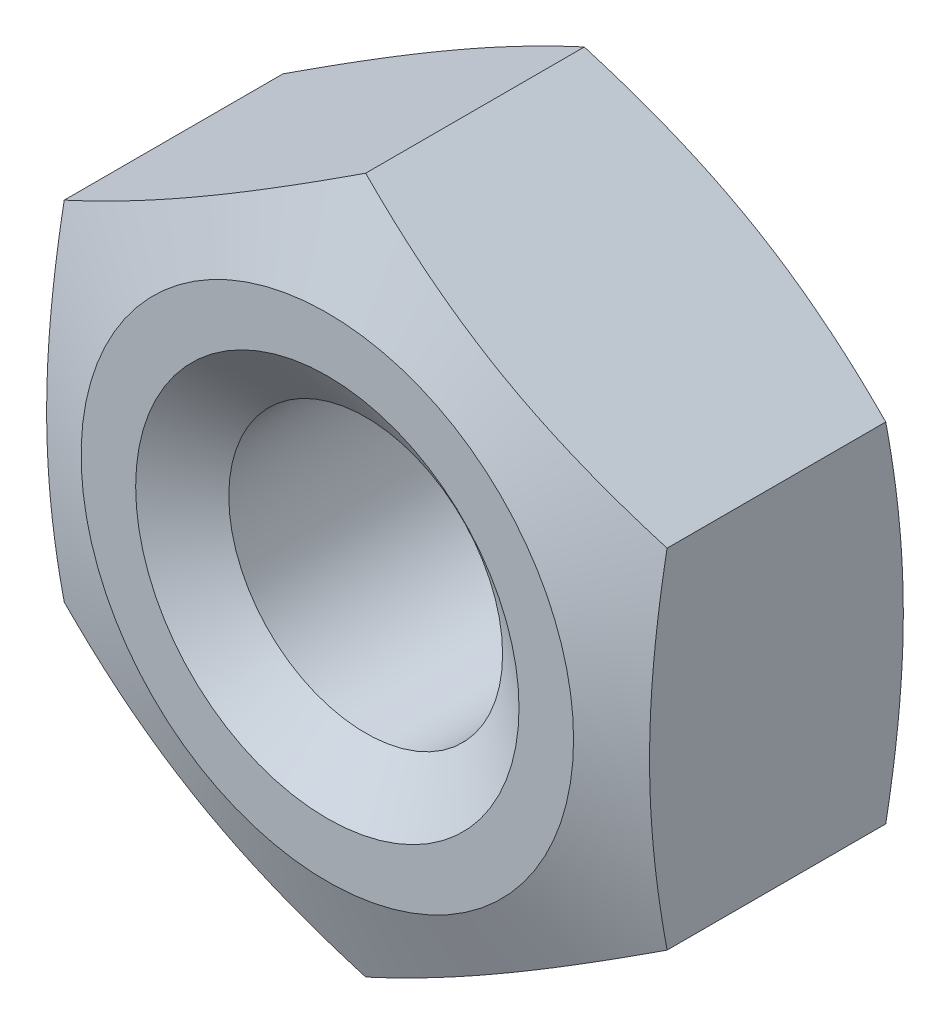
SolidWorks part; units mm, degrees
extrude "BaseNut" add sketch "BaseNutSke" against normal blind 8.5598
sketch "BaseNutSke" plane through (0, 0, 0) normal (0, 0, 1) x (1, 0, 0)
  line L0 (8.7376, 5.0447) -> (-8.7376, -5.0447) construction
  line L1 (-8.7376, 5.0447) -> (8.7376, -5.0447) construction
  line L2 (8.7376, -5.0447) -> (8.6272, -4.9539) construction
  line L3 (0, 10.0893) -> (0, -10.0893) construction
  line L6 (8.7376, 5.0447) -> (8.7376, -5.0447)
  line L7 (-8.7376, 5.0447) -> (-8.7376, -5.0447)
  line L8 (8.7376, 5.0447) -> (0, 10.0893)
  line L9 (0, 10.0893) -> (-8.7376, 5.0447)
  line L10 (-8.7376, -5.0447) -> (0, -10.0893)
  line L11 (0, -10.0893) -> (8.7376, -5.0447)
  circle A0 centre (0, 0) radius 3.9688
  dimension "D4" = 8.7376
  dimension "Tap_drill" = 7.9375
  dimension "D1" = 120
  dimension "D2" = 8.7376
  dimension "D3" = 8.7376
pattern_linear "ThdSchPat" [suppressed]
revolve "ThreadSchematic" [suppressed] cut sketch "ThdSchSke" angle 360 about L6
sketch "ThdSchSke" plane through (0, 0, 0) normal (0, 1, 0) x (1, 0, 0)
  line L0 (-5.5562, 0.0254) -> (-3.9688, 1.137)
  line L1 (-3.9688, 1.137) -> (-1.9844, 1.137)
  line L2 (-1.9844, 1.137) -> (-1.9844, -1.0862)
  line L3 (-1.9844, -1.0862) -> (-3.9688, -1.0862)
  line L4 (-3.9688, -1.0862) -> (-5.5562, 0.0254)
  line L5 (-3.175, 1.5875) -> (3.175, 1.5875) construction
  line L6 (0, 1.5875) -> (0, -2.9874) construction
  line L7 (0, 7.4228) -> (0, 1.1116) construction
  dimension "SideAngle" = 55
  dimension "Thread_major" = 11.1125
  dimension "Advance" = 1.5875
  dimension "D1" = 0.0254
ref_plane "Plane1" through (0, 0, 0) normal (0, 0, 1) x (1, 0, 0)
ref_plane "Plane2" through (0, 0, 0) normal (0, 1, 0) x (1, 0, 0)
ref_plane "Plane3" through (0, 0, 0) normal (1, 0, 0) x (0, 0, -1)
sketch "Sketch4" plane through (0, 0, 0) normal (1, 0, 0) x (0, 0, -1)
  line L0 (8.5598, 8.7376) -> (8.1534, 8.7376)
  line L1 (8.5598, 8.7376) -> (8.5598, 22.7893)
  line L2 (8.1534, 22.7893) -> (8.5598, 22.7893)
  line L3 (8.1534, 22.7893) -> (8.1534, 8.7376)
  line L4 (0, 0) -> (34.925, 0) construction
  line L6 (8.5598, 5.0447) -> (8.5598, 10.0893) construction
  line L7 (0, 8.7376) -> (-12.7, 8.7376)
  line L8 (0, 5.0447) -> (0, 10.0893) construction
  line L9 (1.1113, 10.0893) -> (1.1113, 22.7893)
  line L10 (1.1113, 22.7893) -> (-12.7, 22.7893)
  line L11 (-12.7, 22.7893) -> (-12.7, 8.7376)
  line L12 (0, 8.7376) -> (1.1113, 10.0893)
  line L14 (0, 5.0447) -> (0, -5.0447) construction
  line L15 (8.5598, 10.0893) -> (0, 10.0893) construction
  dimension "D2" = 1.1113
  dimension "D3" = 12.7
  dimension "D4" = 12.7
  dimension "D1" = 8.7376
revolve "Bearing-Face" [suppressed] cut sketch "Sketch4" angle 360 about L4
sketch "Sketch3" plane through (0, 0, 0) normal (1, 0, 0) x (0, 0, -1)
  line L0 (8.5598, 7.1374) -> (7.4486, 10.0893)
  line L1 (7.4486, 10.0893) -> (7.4486, 22.7893)
  line L2 (7.4486, 22.7893) -> (21.2598, 22.7893)
  line L3 (21.2598, 22.7893) -> (21.2598, 7.1374)
  line L4 (21.2598, 7.1374) -> (8.5598, 7.1374)
  line L5 (8.5598, 5.0447) -> (8.5598, 10.0893) construction
  line L6 (8.5598, 10.0893) -> (0, 10.0893) construction
  line L7 (0, 0) -> (38.6776, 0) construction
  line L8 (8.5598, 0) -> (0, 0) construction
  line L9 (4.2799, 10.0893) -> (4.2799, 44.222) construction
  line L10 (1.1113, 22.7893) -> (-12.7, 22.7893)
  line L11 (-12.7, 22.7893) -> (-12.7, 7.1374)
  line L12 (-12.7, 7.1374) -> (0, 7.1374)
  line L13 (0, 7.1374) -> (1.1113, 10.0893)
  line L14 (1.1113, 10.0893) -> (1.1113, 22.7893)
  line L16 (8.5598, 10.0893) -> (0, 10.0893) construction
  dimension "D1" = 7.1374
  dimension "D2" = 1.1113
  dimension "D4" = 12.7
  dimension "D3" = 12.7
revolve "Double-Chamfer" cut sketch "Sketch3" angle 360 about L7
sketch "Sketch5" plane through (0, 0, 0) normal (1, 0, 0) x (0, 0, -1)
  line L0 (8.5344, 5.5563) -> (7.3117, 3.81)
  line L1 (8.5852, 5.5563) -> (8.5344, 5.5563)
  line L2 (8.5852, 5.5563) -> (8.5852, 3.81)
  line L3 (8.5852, 3.81) -> (7.3117, 3.81)
  line L6 (-0.0508, 5.5562) -> (0, 5.5562)
  line L7 (0, 5.5562) -> (1.2227, 3.81)
  line L9 (1.2227, 3.81) -> (-0.0508, 3.81)
  line L10 (-0.0508, 3.81) -> (-0.0508, 5.5562)
  line L11 (25.0375, 0) -> (38.388, 0) construction
  line L12 (8.5598, 0) -> (0, 0) construction
  dimension "D1" = 35
  dimension "D2" = 0.0508
  dimension "ThreadMajor" = 5.5562
  dimension "Offset1" = 8.5852
revolve "EndChamfer" cut sketch "Sketch5" angle 360 about L11
equation "\"D1@Sketch3\" = \"Width_flats@BaseNutSke\" /2"
equation "\"D2@Sketch3\" = \"Thread_major@ThreadCosmetic\" *.1"
equation "\"D1@Sketch4\" = \"D2@BaseNutSke\""
equation "\"D2@Sketch4\" = \"Thread_major@ThreadCosmetic\" *.10"
equation "\"D4@BaseNutSke\" = \"D3@BaseNutSke\""
equation "\"Thread_major@ThdSchSke\" = \"Thread_major@ThreadCosmetic\""
equation "\"Tap_Drill@ThdSchSke\" = \"Tap_drill@BaseNutSke\""
equation "\"OverCut@ThdSchSke\" = \"Tap_Drill@ThdSchSke\" * 0.5"
equation "\"Num_threads@ThdSchPat\" = int(  ( \"Thickness@BaseNut\" - 0.002 ) / \"Advance@ThdSchSke\" + 0.999 )  + 1"
equation "\"Advance@ThdSchPat\" = ( \"Thickness@BaseNut\" - 0.002 ) /  (\"Num_threads@ThdSchPat\" - 1) 'relax it"
equation "' \"Num_threads@ThdSchPat\" = \"Num_threads@ThdSchPat\" - sgn( \"Num_threads@ThdSchPat\" - 1) '---chamfered tips only---"
equation "\"ThreadMajor@Sketch5\" = \"Thread_major@ThreadCosmetic\" * 0.5"
equation "\"ChamferDepth@Sketch5\" = (\"Thread_major@ThreadCosmetic\" - \"Tap_drill@BaseNutSke\") * 0.55"
equation "\"Offset1@Sketch5\" = \"Thickness@BaseNut\" + 0.001"
equation "\"Offset2@Sketch5\" = \"Offset1@Sketch5\" + 0.002"
